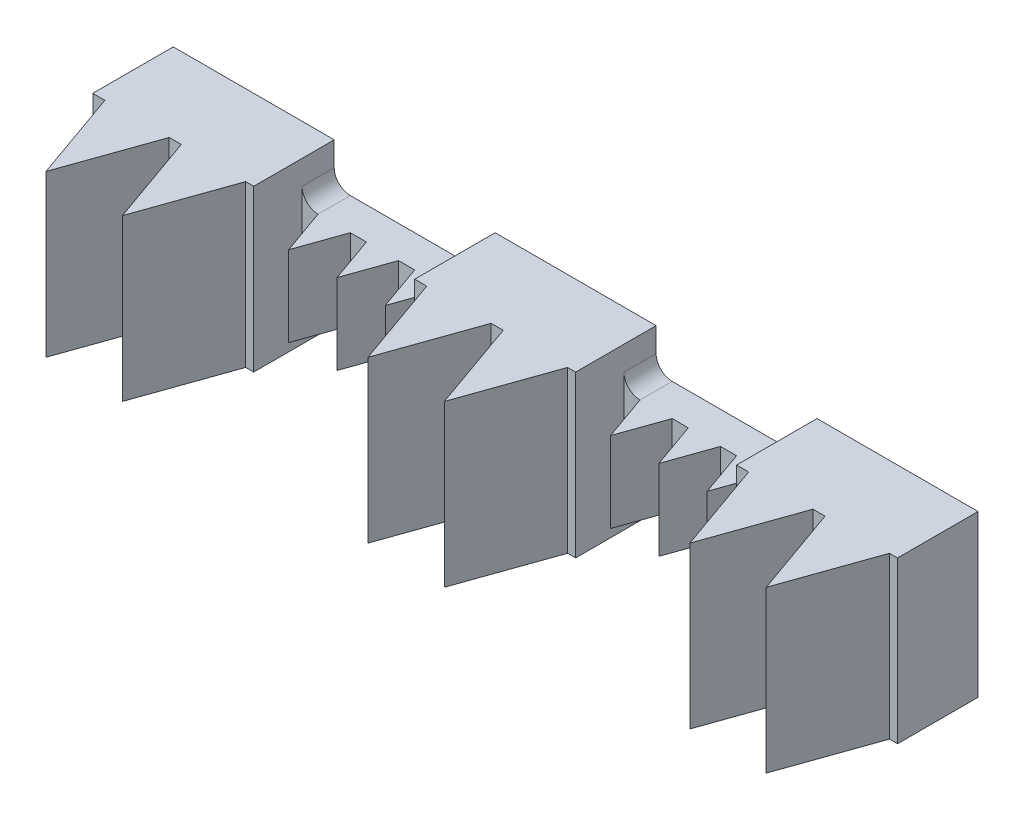
SolidWorks part; units mm, degrees
ref_plane "Front Plane" through (0, 0, 0) normal (0, 0, 1) x (1, 0, 0)
ref_plane "Top Plane" through (0, 0, 0) normal (0, 1, 0) x (1, 0, 0)
ref_plane "Right Plane" through (0, 0, 0) normal (1, 0, 0) x (0, 0, -1)
sketch "Sketch1" plane through (0, 0, 0) normal (0, 0, 1) x (1, 0, 0)
  line L1 (10, -10) -> (-10, -10)
  line L2 (10, -10) -> (10, 10)
  line L3 (10, 10) -> (-10, 10)
  line L4 (-10, -10) -> (-10, 10)
  line L5 (10, -10) -> (-10, 10) construction
  line L6 (10, 10) -> (-10, -10) construction
  point P0 (0, 0)
  dimension "D1" = 20
  dimension "D2" = 20
extrude "Boss-Extrude1" add sketch "Sketch1" along normal blind 10
sketch "Sketch2" plane through (10, 0, 0) normal (1, 0, 0) x (0, 0, -1)
  line L0 (0, -10) -> (0, 10) construction
  line L5 (0, 5) -> (-4, 5)
  line L6 (0, 5) -> (0, -5)
  line L7 (0, -5) -> (-4, -5)
  line L8 (-4, 5) -> (-4, -5)
  dimension "D1" = 10
  dimension "D2" = 5
  dimension "D3" = 4
extrude "Boss-Extrude2" add sketch "Sketch2" along normal blind 20
sketch "Sketch3" plane through (30, 0, 0) normal (1, 0, 0) x (0, 0, -1)
  line L1 (0, 10) -> (-10, 10)
  line L2 (0, 10) -> (0, -10)
  line L3 (0, -10) -> (-10, -10)
  line L4 (-10, 10) -> (-10, -10)
extrude "Boss-Extrude3" add sketch "Sketch3" along normal blind 20
sketch "Sketch4" plane through (50, 0, 0) normal (1, 0, 0) x (0, 0, -1)
  line L0 (0, -10) -> (0, 10) construction
  line L5 (0, 5) -> (-4, 5)
  line L6 (0, 5) -> (0, -5)
  line L7 (0, -5) -> (-4, -5)
  line L8 (-4, 5) -> (-4, -5)
  dimension "D1" = 10
  dimension "D2" = 4
  dimension "D3" = 5
extrude "Boss-Extrude4" add sketch "Sketch4" along normal blind 20
sketch "Sketch5" plane through (70, 0, 0) normal (1, 0, 0) x (0, 0, -1)
  line L1 (0, 10) -> (-10, 10)
  line L2 (0, 10) -> (0, -10)
  line L3 (0, -10) -> (-10, -10)
  line L4 (-10, 10) -> (-10, -10)
extrude "Boss-Extrude5" add sketch "Sketch5" along normal blind 20
sketch "Sketch6" plane through (0, -10, 0) normal (0, -1, 0) x (1, 0, 0)
  line L0 (-8.5, 10) -> (-4.5, 21.3137)
  line L1 (-4.5, 21.3137) -> (-0.5, 10)
  line L2 (-10, 10) -> (10, 10) construction
  line L3 (-0.5, 10) -> (-8.5, 10)
  line L37 (9, 10) -> (1, 10)
  line L38 (1, 10) -> (5, 21.3137)
  line L39 (5, 21.3137) -> (9, 10)
  line L69 (18.5, 10) -> (10.5, 10) [skipped]
  line L70 (10.5, 10) -> (14.5, 21.3137) [skipped]
  line L71 (14.5, 21.3137) -> (18.5, 10) [skipped]
  dimension "D1" = 12
  dimension "D2" = 12
  dimension "D3" = 8
  dimension "D4" = 1.5
  dimension "D5" = 3
extrude "Boss-Extrude6" add sketch "Sketch6" against normal blind 20
sketch "Sketch7" plane through (0, -10, 0) normal (0, -1, 0) x (1, 0, 0)
  line L0 (31.5, 10) -> (35.5, 21.3137)
  line L1 (50, 10) -> (30, 10) construction
  line L2 (35.5, 21.3137) -> (39.5, 10)
  line L3 (71.5, 10) -> (75.5, 21.3137)
  line L4 (90, 10) -> (70, 10) construction
  line L5 (75.5, 21.3137) -> (79.5, 10)
  line L6 (31.5, 10) -> (39.5, 10)
  line L7 (71.5, 10) -> (79.5, 10)
  line L8 (41, 10) -> (49, 10)
  line L9 (45, 21.3137) -> (49, 10)
  line L10 (41, 10) -> (45, 21.3137)
  line L11 (81, 10) -> (89, 10)
  line L12 (85, 21.3137) -> (89, 10)
  line L13 (81, 10) -> (85, 21.3137)
  line L20 (50.5, 10) -> (58.5, 10) [skipped]
  line L21 (54.5, 21.3137) -> (58.5, 10) [skipped]
  line L22 (50.5, 10) -> (54.5, 21.3137) [skipped]
  line L23 (90.5, 10) -> (98.5, 10) [skipped]
  line L24 (94.5, 21.3137) -> (98.5, 10) [skipped]
  line L25 (90.5, 10) -> (94.5, 21.3137) [skipped]
  dimension "D1" = 12
  dimension "D2" = 12
  dimension "D3" = 8
  dimension "D4" = 1.5
  dimension "D5" = 12
  dimension "D6" = 12
  dimension "D7" = 8
  dimension "D8" = 1.5
  dimension "D9" = 3
extrude "Boss-Extrude7" add sketch "Sketch7" against normal blind 20
sketch "Sketch8" plane through (0, -5, 0) normal (0, -1, 0) x (1, 0, 0)
  line L0 (12, 4) -> (14, 9.6569)
  line L1 (30, 4) -> (10, 4) construction
  line L2 (14, 9.6569) -> (16, 4)
  line L3 (12, 4) -> (16, 4)
  line L7 (52, 4) -> (54, 9.6569)
  line L8 (70, 4) -> (50, 4) construction
  line L9 (54, 9.6569) -> (56, 4)
  line L10 (52, 4) -> (56, 4)
  line L89 (18, 4) -> (22, 4)
  line L90 (20, 9.6569) -> (22, 4)
  line L91 (18, 4) -> (20, 9.6569)
  line L92 (58, 4) -> (62, 4)
  line L93 (60, 9.6569) -> (62, 4)
  line L94 (58, 4) -> (60, 9.6569)
  line L95 (24, 4) -> (28, 4)
  line L96 (26, 9.6569) -> (28, 4)
  line L97 (24, 4) -> (26, 9.6569)
  line L98 (64, 4) -> (68, 4)
  line L99 (66, 9.6569) -> (68, 4)
  line L100 (64, 4) -> (66, 9.6569)
  dimension "D1" = 6
  dimension "D2" = 6
  dimension "D3" = 4
  dimension "D4" = 2
  dimension "D5" = 6
  dimension "D6" = 6
  dimension "D7" = 4
  dimension "D8" = 2
extrude "Boss-Extrude8" add sketch "Sketch8" against normal blind 10
sketch "Sketch9" plane through (-10, 0, 0) normal (-1, 0, 0) x (0, 0, 1)
  line L0 (0, 10) -> (0, -10) construction
  line L1 (10, 10) -> (0, 10) construction
  circle A0 centre (7, 0) radius 1.45
  dimension "D1" = 2.9
  dimension "D2" = 7
  dimension "D3" = 10
extrude "Cut-Extrude1" cut sketch "Sketch9" against normal blind 1.5
sketch "Sketch10" plane through (-8.5, 0, 0) normal (-1, 0, 0) x (0, 0, 1)
  line L0 (0, 10) -> (0, -10) construction
  line L1 (1, 9) -> (9, 9)
  line L2 (1, 9) -> (1, -9)
  line L3 (1, -9) -> (9, -9)
  line L4 (9, 9) -> (9, -9)
  line L5 (10, 10) -> (10, -10) construction
  line L6 (10, 10) -> (0, 10) construction
  line L7 (10, -10) -> (0, -10) construction
  dimension "D1" = 1
  dimension "D2" = 1
  dimension "D3" = 1
  dimension "D4" = 1
extrude "Cut-Extrude2" cut sketch "Sketch10" against normal blind 17
sketch "Sketch13" plane through (30, 0, 0) normal (-1, 0, 0) x (0, 0, 1)
  line L0 (10, 10) -> (0, 10) construction
  line L1 (1, 9) -> (9, 9)
  line L2 (1, 9) -> (1, -9)
  line L3 (1, -9) -> (9, -9)
  line L4 (9, 9) -> (9, -9)
  line L5 (0, 10) -> (0, -10) construction
  dimension "D1" = 1
  dimension "D2" = 1
  dimension "D3" = 8
extrude "Cut-Extrude4" cut sketch "Sketch13" against normal blind 19
sketch "Sketch14" plane through (30, 0, 0) normal (-1, 0, 0) x (0, 0, 1)
  line L1 (10, 10) -> (0, 10)
  line L2 (10, 10) -> (10, -10)
  line L3 (10, -10) -> (0, -10)
  line L4 (0, 10) -> (0, -10)
  dimension "D1" = 10
  dimension "D2" = 20
extrude "Boss-Extrude9" add sketch "Sketch14" against normal blind 1
sketch "Sketch15" plane through (70, 0, 0) normal (-1, 0, 0) x (0, 0, 1)
  line L6 (9, 9) -> (1, 9)
  line L7 (9, 9) -> (9, -9)
  line L8 (9, -9) -> (1, -9)
  line L9 (1, 9) -> (1, -9)
  line L10 (0, 10) -> (10, 10) construction
  line L11 (10, 10) -> (10, -10) construction
  dimension "D1" = 18
  dimension "D2" = 1
  dimension "D3" = 1
  dimension "D4" = 8
extrude "Cut-Extrude5" cut sketch "Sketch15" against normal blind 19
sketch "Sketch16" plane through (70, 0, 0) normal (-1, 0, 0) x (0, 0, 1)
  line L1 (10, 10) -> (0, 10)
  line L2 (10, 10) -> (10, -10)
  line L3 (10, -10) -> (0, -10)
  line L4 (0, 10) -> (0, -10)
  dimension "D1" = 20
  dimension "D2" = 10
extrude "Boss-Extrude10" add sketch "Sketch16" against normal blind 1
sketch "Sketch12" plane through (8.5, 0, 0) normal (-1, 0, 0) x (0, 0, 1)
  line L1 (1, 4) -> (3, 4)
  line L2 (1, 4) -> (1, -4)
  line L3 (1, -4) -> (3, -4)
  line L4 (3, 4) -> (3, -4)
  line L6 (10, -10) -> (0, -10) construction
  line L8 (0, -10) -> (0, -5) construction
  point P4 (1, 0)
  dimension "D1" = 6
  dimension "D2" = 8
  dimension "D3" = 2
  dimension "D4" = 1
extrude "Cut-Extrude3" cut sketch "Sketch12" against normal blind 80
sketch "Sketch17" plane through (0, -10, 0) normal (0, -1, 0) x (1, 0, 0)
  line L0 (-7.4393, 10) -> (-4.5, 18.3137)
  line L1 (-4.5, 18.3137) -> (-1.5607, 10)
  line L2 (-1.5607, 10) -> (-7.4393, 10)
  line L3 (-4.5, 21.3137) -> (-8.5, 10) construction
  line L4 (-0.5, 10) -> (-4.5, 21.3137) construction
  line L5 (32.5607, 10) -> (35.5, 18.3137)
  line L6 (35.5, 18.3137) -> (38.4393, 10)
  line L7 (38.4393, 10) -> (32.5607, 10)
  line L8 (72.5607, 10) -> (75.5, 18.3137)
  line L9 (75.5, 18.3137) -> (78.4393, 10)
  line L10 (78.4393, 10) -> (72.5607, 10)
  line L11 (35.5, 21.3137) -> (31.5, 10) construction
  line L12 (39.5, 10) -> (35.5, 21.3137) construction
  line L13 (75.5, 21.3137) -> (71.5, 10) construction
  line L14 (79.5, 10) -> (75.5, 21.3137) construction
  line L15 (7.9393, 10) -> (2.0607, 10)
  line L16 (2.0607, 10) -> (5, 18.3137)
  line L17 (5, 18.3137) -> (7.9393, 10)
  line L18 (47.9393, 10) -> (42.0607, 10)
  line L19 (42.0607, 10) -> (45, 18.3137)
  line L20 (45, 18.3137) -> (47.9393, 10)
  line L21 (87.9393, 10) -> (82.0607, 10)
  line L22 (82.0607, 10) -> (85, 18.3137)
  line L23 (85, 18.3137) -> (87.9393, 10)
  dimension "D1" = 1
  dimension "D2" = 1
  dimension "D3" = 1
  dimension "D4" = 1
  dimension "D5" = 1
  dimension "D6" = 1
  dimension "D7" = 1
  dimension "1" = 1
  dimension "D8" = 0
  dimension "D9" = 1
  dimension "D10" = 1
  dimension "D11" = 1
  dimension "D12" = 1
  dimension "D13" = 0
  dimension "D14" = 2
extrude "Cut-Extrude7" cut sketch "Sketch17" against normal blind 19
sketch "Sketch19" plane through (0, 0, 10) normal (0, 0, 1) x (1, 0, 0)
  line L0 (-7.4393, 9) -> (-7.4393, -10) construction
  line L1 (-7.4393, -9) -> (-1.5607, -9)
  line L2 (-7.4393, -9) -> (-7.4393, 9)
  line L3 (-7.4393, 9) -> (-1.5607, 9)
  line L4 (-1.5607, -9) -> (-1.5607, 9)
  line L5 (-1.5607, 9) -> (-1.5607, -10) construction
  line L6 (-7.4393, -10) -> (-1.5607, -10) construction
  line L7 (-7.4393, 9) -> (-1.5607, 9) construction
  line L8 (32.5607, -10) -> (38.4393, -10) construction
  line L9 (32.5607, 9) -> (38.4393, 9)
  line L10 (32.5607, 9) -> (32.5607, -9)
  line L11 (32.5607, -9) -> (38.4393, -9)
  line L12 (38.4393, 9) -> (38.4393, -9)
  line L13 (78.4393, 9) -> (78.4393, -10) construction
  line L14 (32.5607, 9) -> (32.5607, -10) construction
  line L15 (72.5607, 9) -> (72.5607, -10) construction
  line L16 (38.4393, 9) -> (38.4393, -10) construction
  line L17 (32.5607, 9) -> (38.4393, 9) construction
  line L18 (72.5607, -10) -> (78.4393, -10) construction
  line L19 (78.4393, 9) -> (72.5607, 9)
  line L20 (78.4393, 9) -> (78.4393, -9)
  line L21 (78.4393, -9) -> (72.5607, -9)
  line L22 (72.5607, 9) -> (72.5607, -9)
  line L23 (72.5607, 9) -> (78.4393, 9) construction
  line L24 (2.0607, -9) -> (2.0607, 9)
  line L25 (2.0607, -9) -> (7.9393, -9)
  line L26 (7.9393, -9) -> (7.9393, 9)
  line L27 (2.0607, 9) -> (7.9393, 9)
  line L28 (42.0607, 9) -> (42.0607, -9)
  line L29 (42.0607, 9) -> (47.9393, 9)
  line L30 (47.9393, 9) -> (47.9393, -9)
  line L31 (42.0607, -9) -> (47.9393, -9)
  line L32 (87.9393, 9) -> (87.9393, -9)
  line L33 (87.9393, 9) -> (82.0607, 9)
  line L34 (82.0607, 9) -> (82.0607, -9)
  line L35 (87.9393, -9) -> (82.0607, -9)
  dimension "D1" = 0
  dimension "D2" = 0
  dimension "D3" = 1
  dimension "D4" = 0
  dimension "D5" = 1
  dimension "D6" = 0
  dimension "D7" = 0
  dimension "D8" = 0
  dimension "D9" = 1
  dimension "D10" = 0
  dimension "D11" = 0
  dimension "D12" = 0
  dimension "D13" = 2
extrude "Cut-Extrude8" cut sketch "Sketch19" against normal blind 5
sketch "Sketch21" plane through (0, -10, 0) normal (0, -1, 0) x (1, 0, 0)
  line L0 (-8.5, 10) -> (-4.5, 21.3137)
  line L1 (-4.5, 21.3137) -> (-0.5, 10)
  line L2 (-0.5, 10) -> (-8.5, 10)
  line L3 (31.5, 10) -> (35.5, 21.3137)
  line L4 (35.5, 21.3137) -> (39.5, 10)
  line L5 (39.5, 10) -> (31.5, 10)
  line L6 (71.5, 10) -> (75.5, 21.3137)
  line L7 (75.5, 21.3137) -> (79.5, 10)
  line L8 (71.5, 10) -> (79.5, 10)
  line L9 (9, 10) -> (1, 10)
  line L10 (1, 10) -> (5, 21.3137)
  line L11 (5, 21.3137) -> (9, 10)
  line L12 (49, 10) -> (41, 10)
  line L13 (41, 10) -> (45, 21.3137)
  line L14 (45, 21.3137) -> (49, 10)
  line L15 (81, 10) -> (89, 10)
  line L16 (85, 21.3137) -> (89, 10)
  line L17 (81, 10) -> (85, 21.3137)
  dimension "D1" = 2
extrude "Boss-Extrude12" add sketch "Sketch21" against normal blind 1
sketch "Sketch22" plane through (0, -5, 0) normal (0, -1, 0) x (1, 0, 0)
  line L0 (12.8485, 4) -> (14, 7.2569)
  line L1 (14, 7.2569) -> (15.1515, 4)
  line L2 (15.1515, 4) -> (12.8485, 4)
  line L3 (52.8485, 4) -> (54, 7.2569)
  line L4 (54, 7.2569) -> (55.1515, 4)
  line L5 (55.1515, 4) -> (52.8485, 4)
  line L6 (14, 9.6569) -> (12, 4) construction
  line L7 (16, 4) -> (14, 9.6569) construction
  line L8 (54, 9.6569) -> (52, 4) construction
  line L9 (56, 4) -> (54, 9.6569) construction
  line L10 (21.1515, 4) -> (18.8485, 4)
  line L11 (18.8485, 4) -> (20, 7.2569)
  line L12 (20, 7.2569) -> (21.1515, 4)
  line L13 (61.1515, 4) -> (58.8485, 4)
  line L14 (58.8485, 4) -> (60, 7.2569)
  line L15 (60, 7.2569) -> (61.1515, 4)
  line L16 (27.1515, 4) -> (24.8485, 4)
  line L17 (24.8485, 4) -> (26, 7.2569)
  line L18 (26, 7.2569) -> (27.1515, 4)
  line L19 (67.1515, 4) -> (64.8485, 4)
  line L20 (64.8485, 4) -> (66, 7.2569)
  line L21 (66, 7.2569) -> (67.1515, 4)
  dimension "D1" = 0.8
  dimension "D2" = 0.8
  dimension "D3" = 0.8
  dimension "D4" = 0.8
  dimension "D5" = 0
  dimension "D6" = 0.8
  dimension "D7" = 0.8
  dimension "D8" = 0.8
  dimension "D9" = 0.8
  dimension "D10" = 0
  dimension "D11" = 3
extrude "Cut-Extrude10" cut sketch "Sketch22" against normal blind 9
sketch "Sketch23" plane through (0, 0, 4) normal (0, 0, 1) x (1, 0, 0)
  line L0 (12.8485, 4) -> (12.8485, -5) construction
  line L1 (12.8485, -4) -> (15.1515, -4)
  line L2 (12.8485, -4) -> (12.8485, 4)
  line L3 (12.8485, 4) -> (15.1515, 4)
  line L4 (15.1515, -4) -> (15.1515, 4)
  line L5 (12.8485, -5) -> (15.1515, -5) construction
  line L6 (12.8485, 4) -> (15.1515, 4) construction
  line L7 (52.8485, -5) -> (55.1515, -5) construction
  line L8 (52.8485, -4) -> (55.1515, -4)
  line L9 (52.8485, -4) -> (52.8485, 4)
  line L10 (52.8485, 4) -> (55.1515, 4)
  line L11 (55.1515, -4) -> (55.1515, 4)
  line L12 (52.8485, 4) -> (55.1515, 4) construction
  line L13 (52.8485, 4) -> (52.8485, -5) construction
  line L14 (55.1515, 4) -> (55.1515, -5) construction
  line L15 (18.8485, -4) -> (18.8485, 4)
  line L16 (18.8485, -4) -> (21.1515, -4)
  line L17 (21.1515, -4) -> (21.1515, 4)
  line L18 (18.8485, 4) -> (21.1515, 4)
  line L19 (58.8485, -4) -> (58.8485, 4)
  line L20 (58.8485, -4) -> (61.1515, -4)
  line L21 (61.1515, -4) -> (61.1515, 4)
  line L22 (58.8485, 4) -> (61.1515, 4)
  line L23 (24.8485, -4) -> (24.8485, 4)
  line L24 (24.8485, -4) -> (27.1515, -4)
  line L25 (27.1515, -4) -> (27.1515, 4)
  line L26 (24.8485, 4) -> (27.1515, 4)
  line L27 (64.8485, -4) -> (64.8485, 4)
  line L28 (64.8485, -4) -> (67.1515, -4)
  line L29 (67.1515, -4) -> (67.1515, 4)
  line L30 (64.8485, 4) -> (67.1515, 4)
  dimension "D1" = 0
  dimension "D2" = 0
  dimension "D3" = 1
  dimension "D4" = 0
  dimension "D5" = 1
  dimension "D6" = 0
  dimension "D7" = 0
  dimension "D8" = 0
  dimension "D9" = 3
extrude "Cut-Extrude11" cut sketch "Sketch23" against normal blind 3
sketch "Sketch24" plane through (0, -5, 0) normal (0, -1, 0) x (1, 0, 0)
  line L0 (12, 4) -> (14, 9.6569)
  line L1 (14, 9.6569) -> (16, 4)
  line L2 (16, 4) -> (12, 4)
  line L3 (52, 4) -> (54, 9.6569)
  line L4 (54, 9.6569) -> (56, 4)
  line L5 (56, 4) -> (52, 4)
  line L6 (22, 4) -> (18, 4)
  line L7 (18, 4) -> (20, 9.6569)
  line L8 (20, 9.6569) -> (22, 4)
  line L9 (62, 4) -> (58, 4)
  line L10 (58, 4) -> (60, 9.6569)
  line L11 (60, 9.6569) -> (62, 4)
  line L12 (28, 4) -> (24, 4)
  line L13 (24, 4) -> (26, 9.6569)
  line L14 (26, 9.6569) -> (28, 4)
  line L15 (68, 4) -> (64, 4)
  line L16 (64, 4) -> (66, 9.6569)
  line L17 (66, 9.6569) -> (68, 4)
  dimension "D1" = 3
extrude "Boss-Extrude13" add sketch "Sketch24" against normal blind 1
fillet "Fillet3" radius 2 1 edges at (10, -5, 2)
fillet "Fillet4" radius 2 7 edges at (30, 5, 2) (50, 5, 2) (10, 5, 2) (70, 5, 2) (50, -5, 2) (70, -5, 2) (30, -5, 2)
